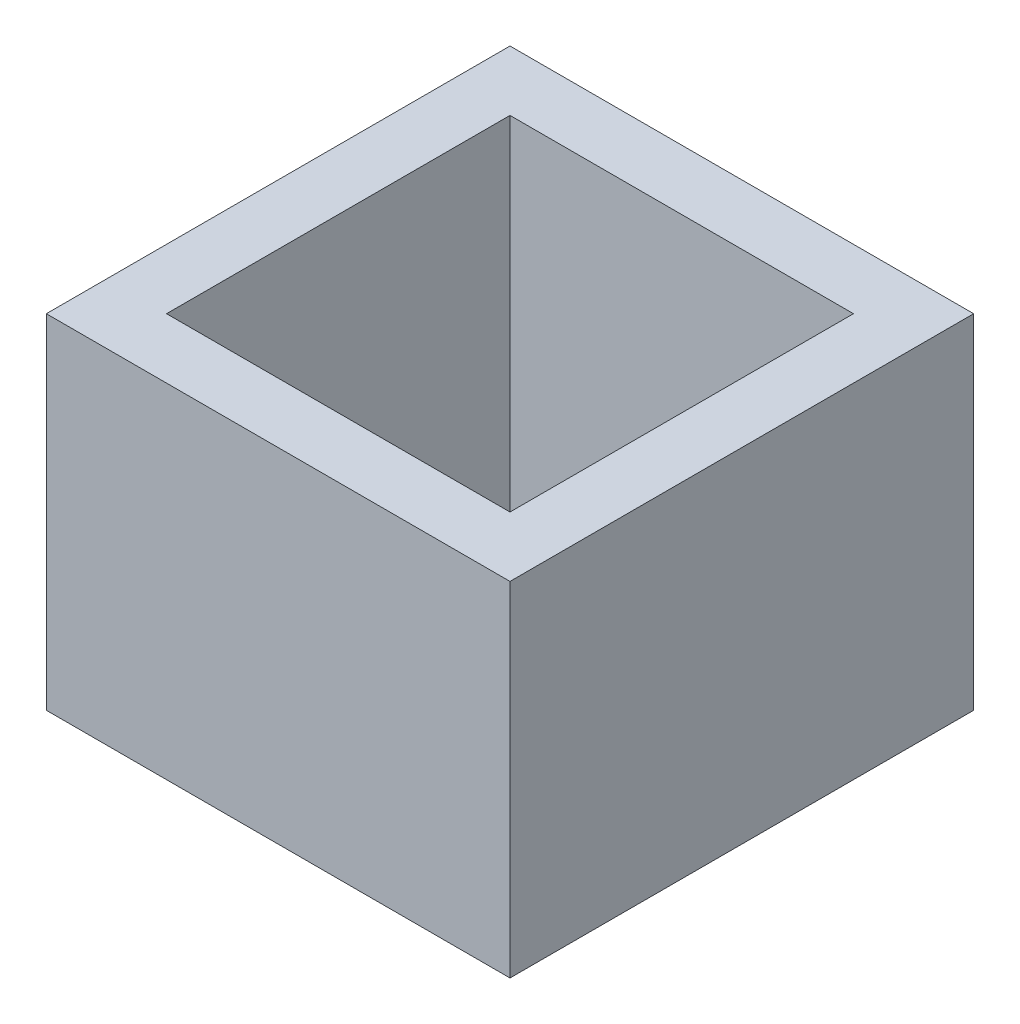
SolidWorks part; units mm, degrees
ref_plane "Front Plane" through (0, 0, 0) normal (0, 0, 1) x (1, 0, 0)
ref_plane "Top Plane" through (0, 0, 0) normal (0, 1, 0) x (1, 0, 0)
ref_plane "Right Plane" through (0, 0, 0) normal (1, 0, 0) x (0, 0, -1)
sketch "Sketch1" plane through (0, 0, 0) normal (0, 1, 0) x (1, 0, 0)
  line L0 (6.75, 6.75) -> (-6.75, 6.75)
  line L1 (5, -5) -> (-5, -5)
  line L2 (5, -5) -> (5, 5)
  line L3 (5, 5) -> (-5, 5)
  line L4 (-5, -5) -> (-5, 5)
  line L5 (5, -5) -> (-5, 5) construction
  line L6 (5, 5) -> (-5, -5) construction
  line L7 (-6.75, -6.75) -> (-6.75, 6.75)
  line L8 (6.75, -6.75) -> (-6.75, -6.75)
  line L9 (6.75, -6.75) -> (6.75, 6.75)
  point P0 (0, 0)
  dimension "D3" = 10
  dimension "D1" = 1.75
extrude "Boss-Extrude1" add sketch "Sketch1" along normal blind 10
